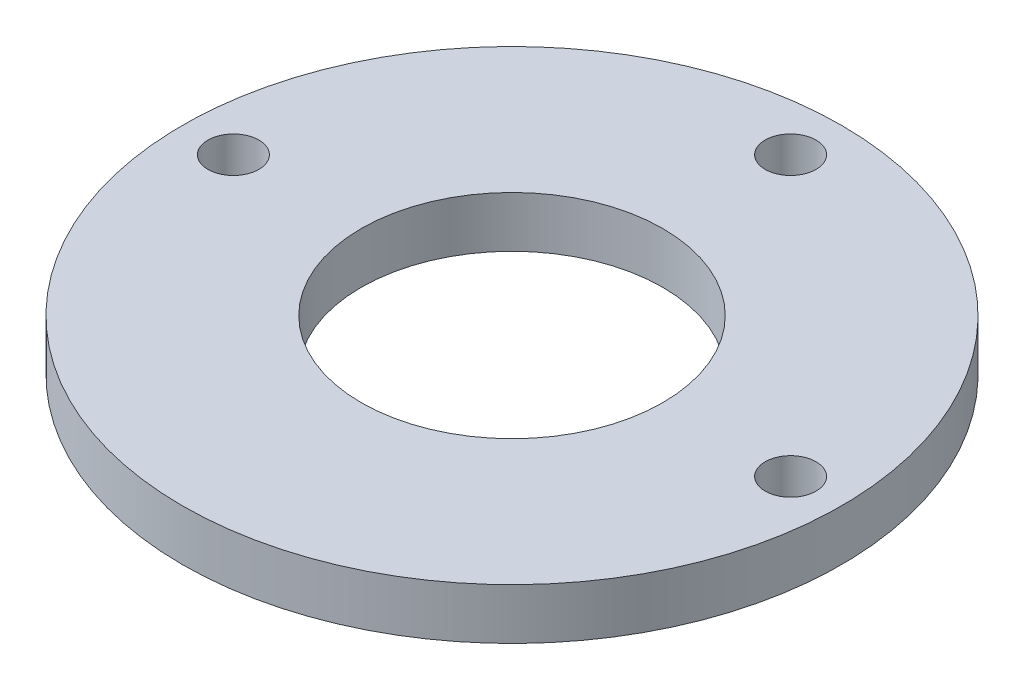
SolidWorks part; units mm, degrees
material "6061-T6 (SS)"
ref_plane "Front Plane" through (0, 0, 0) normal (0, 0, 1) x (1, 0, 0)
ref_plane "Top Plane" through (0, 0, 0) normal (0, 1, 0) x (1, 0, 0)
ref_plane "Right Plane" through (0, 0, 0) normal (1, 0, 0) x (0, 0, -1)
sketch "Sketch1" plane through (0, 0, 0) normal (0, 1, 0) x (1, 0, 0)
  line L0 (-178.6964, 71.4425) -> (-172.1464, 71.4425) construction
  line L1 (-172.1464, 71.4425) -> (-165.5964, 71.4425) construction
  line L2 (-181.8714, 112.7175) -> (-162.9056, 93.7518)
  line L3 (-140.5964, 96.4425) -> (-140.5964, 102.9925) construction
  line L4 (-140.5964, 102.9925) -> (-140.5964, 109.5425) construction
  line L5 (-140.5964, 71.4425) -> (-181.8714, 112.7175)
  line L6 (-140.5964, 71.4425) -> (-162.9056, 93.7518)
  line L7 (-140.5964, 71.4425) -> (-165.1507, 46.8883)
  line L8 (-140.5964, 71.4425) -> (-116.0421, 95.9968)
  line L9 (-140.5964, 71.4425) -> (-165.1507, 95.9968)
  line L10 (0, 0) -> (0, 34.725)
  line L11 (0, 0) -> (34.725, 0)
  line L12 (0, 0) -> (-34.725, 0)
  circle A1 centre (0, 0) radius 25 construction
  circle A7 centre (-140.5964, 71.4425) radius 26.25
  circle A8 centre (-140.5964, 71.4425) radius 25 construction
  circle A9 centre (-140.5964, 71.4425) radius 38.1
  circle A10 centre (-140.5964, 71.4425) radius 31.55
  circle A11 centre (-140.5964, 71.4425) radius 34.725
  circle A12 centre (-165.1507, 95.9968) radius 3.175
  circle A13 centre (-116.0421, 95.9968) radius 3.175
  circle A14 centre (-165.1507, 46.8883) radius 3.175
  circle A15 centre (-140.5964, 71.4425) radius 34.725
  circle A16 centre (0, 0) radius 31.55
  circle A18 centre (0, 34.725) radius 3.175
  circle A19 centre (34.725, 0) radius 3.175
  circle A20 centre (-34.725, 0) radius 3.175
  circle A21 centre (0, 0) radius 41.075
  circle A22 centre (0, 0) radius 26.25
  circle A23 centre (0, 0) radius 18.796
  point P29 (-140.5964, 71.4425)
  dimension "D1" = 76.2
  dimension "D2" = 6.35
  dimension "D3" = 6.35
  dimension "D4" = 52.5
  dimension "D5" = 6.35
  dimension "D6" = 6.35
  dimension "D8" = 6.35
  dimension "D9" = 6.35
  dimension "D7" = 37.592
extrude "Boss-Extrude2" add sketch "Sketch1" along normal blind 6.35 contours A21 A20 A16 A18 A19 | A22 L10 A16 L12 | A22 L11 A16 L10 | A23 L11 A22 L10 | A23 L10 A22 L12 | A22 L12 A16 L11 | A23 L12 A22 L11
